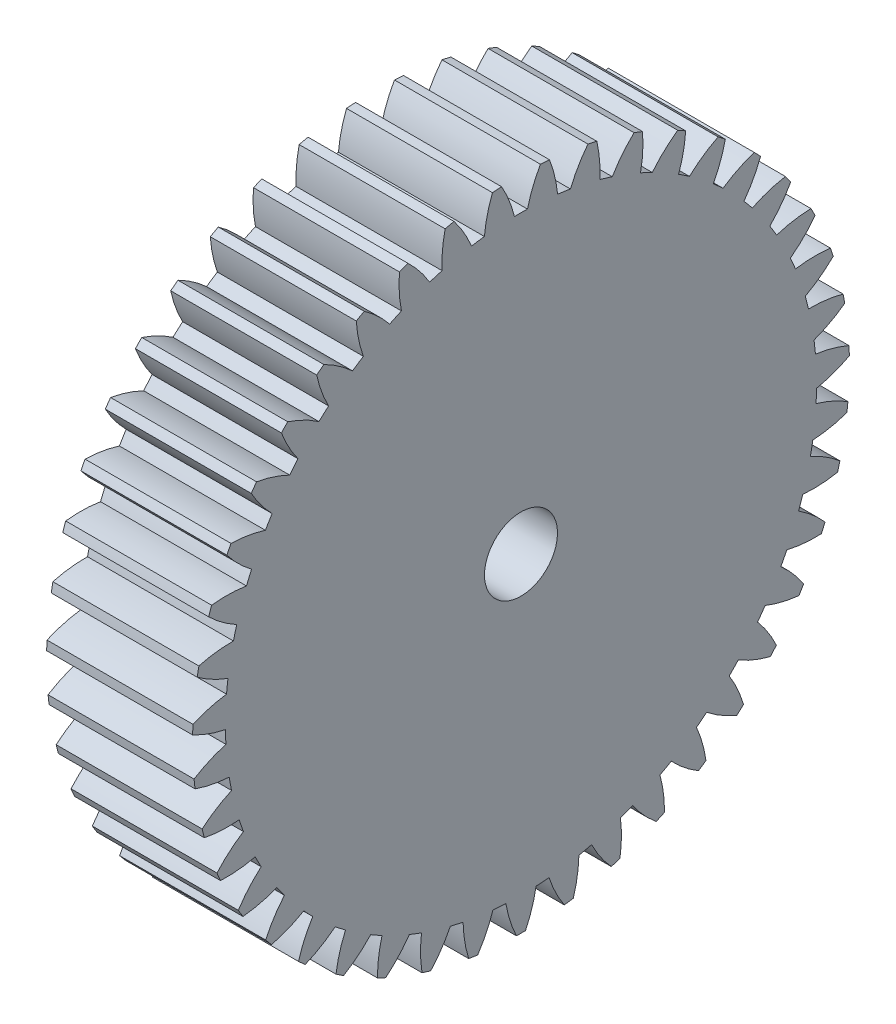
SolidWorks part; units mm, degrees
ref_plane "Plane1" through (0, 0, 0) normal (0, 0, 1) x (1, 0, 0)
ref_plane "Plane2" through (0, 0, 0) normal (0, 1, 0) x (1, 0, 0)
ref_plane "Plane3" through (0, 0, 0) normal (1, 0, 0) x (0, 0, -1)
other "Configuration Table"
sketch "HoldingSke" plane through (0, 0, 0) normal (0, 1, 0) x (1, 0, 0)
  line L0 (0, 0) -> (0.7314, -0.682)
  line L1 (-15, 0) -> (100, 0) construction
  line L2 (0, 0) -> (-2.1039, 2.3779)
  line L3 (0, 0) -> (-11.863, 4.5341)
  line L4 (0, 0) -> (6.316, 5.8897)
  line L5 (0, 0) -> (-46.8476, -17.4728)
  line L6 (0, 0) -> (-8.2896, -5.593)
  line L7 (-2.1039, 2.3779) -> (8.6586, 51.2059)
  line L8 (-76.2, 54.61) -> (-75.3, 54.61)
  line L9 (-71.009, 38.7566) -> (-53.1078, 45.2721)
  line L10 (-76.2, 71.12) -> (104.1128, 71.12)
  line L11 (0, 0) -> (-10, 0)
  line L12 (-76.2, 101.6) -> (-76.162, 101.6)
  line L13 (24.9733, 27.94) -> (52.9518, 28.4284)
  line L14 (24.9733, 27.94) -> (24.9743, 27.94)
  line L15 (24.9733, 27.94) -> (100.4006, 29.5858)
  line L16 (-63.627, -1) -> (-12.827, -1)
  circle A0 centre (0, 0) radius 2.5
  circle A1 centre (0, 0) radius 20.249
  circle A2 centre (0, 0) radius 37.5
  circle A3 centre (0, 0) radius 2.5
  dimension "MHD" = 40.498
  dimension "Hub_dia" = 75
  dimension "Bore" = 5
  dimension "MBD" = 5
  dimension "Num_teeth" = 43
  dimension "Pitch" = 1
  dimension "Overall_len" = 50
  dimension "Show_teeth" = 43
  dimension "Thickness" = 10
  dimension "OAL" = 50.0001
  dimension "T_dim" = 0.9
  dimension "Ap" = 20
  dimension "H" = 19.05
  dimension "Pitch_radius" = 180.3128
  dimension "Width" = 10
  dimension "Backlash" = 0.038
  dimension "Addendum_fac" = 1
  dimension "Dedendum_fac" = 1.25
  dimension "Clearance_fac" = 0.25
  dimension "Dedendum_add" = 0.001
  dimension "Module" = 1
sketch "BasProSke" plane through (0, 0, 0) normal (0, 1, 0) x (1, 0, 0)
  line L0 (-10, 0) -> (60, 0) construction
  line L1 (0, 0) -> (0, 22.5)
  line L2 (0, 0) -> (10, 0)
  line L3 (10, 0) -> (10, 22.5)
  line L4 (10, 22.5) -> (0, 22.5)
  dimension "Thickness" = 10
  dimension "Diameter" = 45
revolve "Base-Revolve" add sketch "BasProSke" angle 360 about L0
sketch "TooCutSke" plane through (0, 0, 0) normal (1, 0, 0) x (0, 0, -1)
  line L1 (0, 0) -> (0, 107) construction
  line L2 (0, 0) -> (-0.8517, 21.4831) construction
  line L3 (0, 0) -> (-3.137, 42.8613) construction
  line L4 (-0.8517, 21.4831) -> (-1.5685, 21.4307) construction
  arc A0 (0.4449, 20.2441) -> (-0.4449, 20.2441) centre (0, 0) ccw
  arc A1 (1.3459, 22.4852) -> (-1.3459, 22.4852) centre (0, 0) ccw
  circle A2 centre (0, 0) radius 21.5 construction
  circle A3 centre (0, 0) radius 20.2034 construction
  arc A4 (-0.4449, 20.2441) -> (-1.3459, 22.4852) centre (-8.7955, 18.1883) ccw
  arc A5 (1.3459, 22.4852) -> (0.4449, 20.2441) centre (8.7955, 18.1883) ccw
  dimension "Root_dia" = 40.498
  dimension "Overcut_dia" = 45.0508
  dimension "Pitch_dia" = 43
  dimension "Base_dia" = 40.4068
  dimension "Flank_rad" = 8.6
  dimension "Half_ang" = 4.186
  dimension "Half_CT" = 0.7187
extrude "ToothCut" cut sketch "TooCutSke" along normal through all
fillet "Breaks" [suppressed] radius 0.02
fillet "RootFillets" [suppressed] radius 0.251
pattern_circular "TeethCuts" count 43 every 8.372 about axis through (-10, 0, 0) along (1, 0, 0) of "ToothCut", "RootFillets", "Breaks"
sketch "HubNeaOneSke" plane through (0, 0, 0) normal (-1, 0, 0) x (0, 0, 1)
  circle A0 centre (0, 0) radius 20.249
  dimension "Diameter" = 40.498
extrude "HubNearOne" [suppressed] add sketch "HubNeaOneSke" along normal blind 40.0001
sketch "HubNeaBotSke" plane through (0, 0, 0) normal (-1, 0, 0) x (0, 0, 1)
  circle A0 centre (0, 0) radius 20.249
  dimension "Diameter" = 40.498
extrude "HubNearBoth" [suppressed] add sketch "HubNeaBotSke" along normal blind 20
ref_plane "FarPln" through (10, 0, 0) normal (1, 0, 0) x (0, 0, -1)
sketch "HubFarSke" plane through (10, 0, 0) normal (1, 0, 0) x (0, 0, -1)
  circle A0 centre (0, 0) radius 20.249
  dimension "Diameter" = 40.498
extrude "HubFar" [suppressed] add sketch "HubFarSke" along normal blind 20
sketch "BorSke" plane through (0, 0, 0) normal (1, 0, 0) x (0, 0, -1)
  circle A0 centre (0, 0) radius 2.5
  dimension "Diameter" = 5
extrude "Bore" cut sketch "BorSke" along normal mid plane 100.0001
sketch "KeySke" plane through (0, 0, 0) normal (1, 0, 0) x (0, 0, -1)
  line L0 (-1, 0) -> (-1, 3.4)
  line L1 (-1, 3.4) -> (1, 3.4)
  line L2 (1, 3.4) -> (1, 0)
  line L3 (0, 0) -> (0, 34) construction
  line L4 (-1, 0) -> (1, 0)
  dimension "Offset" = 3.4
  dimension "Width" = 2
extrude "Keyway" [suppressed] cut sketch "KeySke" along normal mid plane 100.0001
pattern_circular "Keyway2" [suppressed] count 2 every 90 about axis through (-10, 0, 0) along (1, 0, 0)
equation "' \"Module@HoldingSke\" = 6.35"
equation "' \"Num_teeth@HoldingSke\" = 12"
equation "' \"Ap@HoldingSke\" =  20"
equation "' \"Ap@HoldingSke\" = 20"
equation "' \"Width@HoldingSke\" = 0.5 * 25.4"
equation "' \"Hub_dia@HoldingSke\"= 1 * 25.4"
equation "' \"Hub_dia@HoldingSke\" = 1 * 25.4"
equation "' \"Overall_len@HoldingSke\" = 1.0 * 25.4"
equation "' \"Bore@HoldingSke\" = 0.75 * 25.4"
equation "' \"T_dim@HoldingSke\" = 0.1 * 25.4"
equation "' \"Width@KeySke\" = 0.25 * 25.4"
equation "' \"Show_teeth@HoldingSke\" = 13"
equation "' \"Backlash@HoldingSke\" = 0.009 * 25.4"
equation "' \"Addendum_fac@HoldingSke\" = 1.0"
equation "' \"Dedendum_fac@HoldingSke\" = 1.25"
equation "' \"Dedendum_add@HoldingSke\" = 0.00005 * 25.4"
equation "' \"Clearance_fac@HoldingSke\" = 0.25"
equation "\"Pitch@HoldingSke\" = 1 / \"Module@HoldingSke\""
equation "\"Overcut_dia@TooCutSke\" = (\"Num_teeth@HoldingSke\" + 2 * \"Addendum_fac@HoldingSke\") / \"Pitch@HoldingSke\" + 0.002 * 25.4"
equation "\"Pitch_dia@TooCutSke\" = \"Num_teeth@HoldingSke\" / \"Pitch@HoldingSke\""
equation "\"Base_dia@TooCutSke\" = \"Num_teeth@HoldingSke\" / \"Pitch@HoldingSke\" * cos((\"Ap@HoldingSke\"  * 3.14159265 / 180))"
equation "\"Root_dia@TooCutSke\" = (\"Num_teeth@HoldingSke\" + 2) / \"Pitch@HoldingSke\" - 2 * (\"Addendum_fac@HoldingSke\" + \"Dedendum_fac@HoldingSke\") / \"Pitch@HoldingSke\" - \"Dedendum_add@HoldingSke\" * 2"
equation "\"Half_ang@TooCutSke\" = 180 / \"Num_teeth@HoldingSke\""
equation "\"Half_CT@TooCutSke\" = \"Num_teeth@HoldingSke\" / \"Pitch@HoldingSke\" * sin((3.14159265 / 2 / \"Num_teeth@HoldingSke\")) / 2 - 7 * \"Backlash@HoldingSke\" / 4"
equation "\"Flank_rad@TooCutSke\" = \"Num_teeth@HoldingSke\" / \"Pitch@HoldingSke\" / 5"
equation "\"Radius@RootFillets\" = \"Clearance_fac@HoldingSke\" / \"Pitch@HoldingSke\" + \"Dedendum_add@HoldingSke\""
equation "\"Break_rad@Breaks\" = 0.02 / \"Pitch@HoldingSke\""
equation "\"Thickness@HoldingSke\" = \"Width@HoldingSke\""
equation "\"OAL@HoldingSke\" = \"Thickness@HoldingSke\""
equation "\"MHD@HoldingSke\" = (\"Num_teeth@HoldingSke\" + 2) / \"Pitch@HoldingSke\" - 2 * (\"Addendum_fac@HoldingSke\" + \"Dedendum_fac@HoldingSke\")  / \"Pitch@HoldingSke\" - \"Dedendum_add@HoldingSke\" * 2"
equation "\"MBD@HoldingSke\" = (\"Num_teeth@HoldingSke\" + 2) / \"Pitch@HoldingSke\" - 2 * (\"Addendum_fac@HoldingSke\" + \"Dedendum_fac@HoldingSke\")  / \"Pitch@HoldingSke\" - \"Dedendum_add@HoldingSke\" * 2 - 0.002 * 25.4"
equation "\"MHD@HoldingSke\" = ((sgn( \"MHD@HoldingSke\" - \"Hub_dia@HoldingSke\" )-1)*( \"MHD@HoldingSke\" - \"Hub_dia@HoldingSke\" ))/-2+ \"Hub_dia@HoldingSke\""
equation "\"MBD@HoldingSke\" = ((sgn( \"MBD@HoldingSke\" - \"Bore@HoldingSke\" )-1)*( \"MBD@HoldingSke\" - \"Bore@HoldingSke\" ))/-2+ \"Bore@HoldingSke\""
equation "\"OAL@HoldingSke\" = ((sgn( \"OAL@HoldingSke\" - \"Overall_len@HoldingSke\" )+1)*( \"OAL@HoldingSke\" - \"Overall_len@HoldingSke\" ))/2 + \"Overall_len@HoldingSke\" + 0.000002 * 25.4"
equation "\"Num_teeth@TeethCuts\" = int( \"Show_teeth@HoldingSke\" ) + 1"
equation "\"Num_teeth@TeethCuts\" = ((sgn( \"Num_teeth@TeethCuts\" - \"Num_teeth@HoldingSke\" )-1)*( \"Num_teeth@TeethCuts\" - \"Num_teeth@HoldingSke\" ))/-2+ \"Num_teeth@HoldingSke\""
equation "\"Num_teeth@TeethCuts\" = ((sgn( \"Num_teeth@TeethCuts\" - 2.0)+1)*( \"Num_teeth@TeethCuts\" - 2.0))/2 +2.0"
equation "\"Angle@TeethCuts\" = 360.0 / \"Num_teeth@HoldingSke\""
equation "\"Diameter@BasProSke\" = (\"Num_teeth@HoldingSke\" + 2 * \"Addendum_fac@HoldingSke\") / \"Pitch@HoldingSke\""
equation "\"Thickness@BasProSke\"  = \"Thickness@HoldingSke\""
equation "' \"Fillet_rad@BasProSke\" =  \"Thickness@HoldingSke\" * 0.05"
equation "' \"Fillet_rad@BasProSke\" = \"Thickness@HoldingSke\" * 0.05"
equation "\"MHD@HoldingSke\" = ((sgn( \"MHD@HoldingSke\" - \"Root_dia@TooCutSke\" )-1)*( \"MHD@HoldingSke\" - \"Root_dia@TooCutSke\" ))/-2+ \"Root_dia@TooCutSke\""
equation "\"Diameter@HubNeaOneSke\" = \"MHD@HoldingSke\""
equation "\"Length@HubNearOne\" = \"OAL@HoldingSke\" - \"Thickness@BasProSke\""
equation "\"Diameter@HubNeaBotSke\" = \"MHD@HoldingSke\""
equation "\"Length@HubNearBoth\" = ( \"OAL@HoldingSke\" - \"Thickness@BasProSke\" ) / 2.0"
equation "\"Thickness@FarPln\" = \"Thickness@BasProSke\""
equation "\"Diameter@HubFarSke\" = \"MHD@HoldingSke\""
equation "\"Length@HubFar\" = ( \"OAL@HoldingSke\" - \"Thickness@BasProSke\" ) / 2.0"
equation "\"Diameter@BorSke\" = \"MBD@HoldingSke\""
equation "\"D1@Bore\" = \"OAL@HoldingSke\" * 2.0"
equation "\"D1@Keyway\" = \"OAL@HoldingSke\" * 2.0"
equation "\"Offset@KeySke\" = \"T_dim@HoldingSke\" + \"MBD@HoldingSke\" / 2.0"
